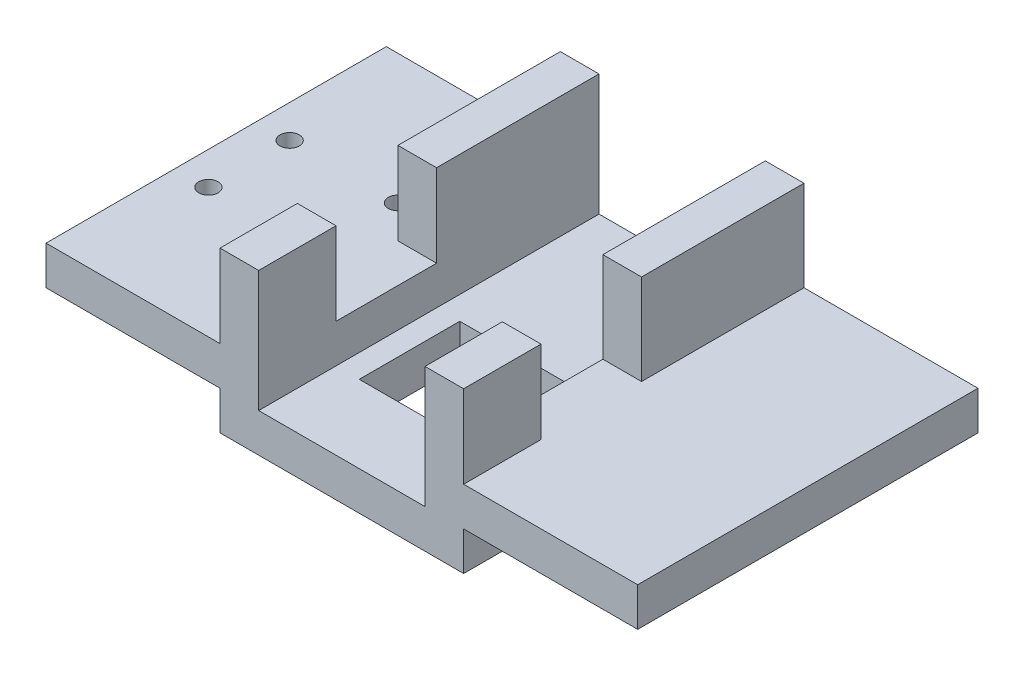
SolidWorks part; units mm, degrees
ref_plane "Plan de face" through (0, 0, 0) normal (0, 0, 1) x (1, 0, 0)
ref_plane "Plan de dessus" through (0, 0, 0) normal (0, 1, 0) x (1, 0, 0)
ref_plane "Plan de droite" through (0, 0, 0) normal (1, 0, 0) x (0, 0, -1)
sketch "Sketch1" plane through (0, 0, 0) normal (0, 0, 1) x (1, 0, 0)
  line L1 (0, -4.1444) -> (10, -4.1444)
  line L2 (10, -4.1444) -> (10, -35.5315)
  line L3 (0, -4.1444) -> (0, -25.5315)
  line L4 (63, -45.5315) -> (0, -45.5315)
  line L5 (0, -25.5315) -> (-45, -25.5315)
  line L6 (10, -35.5315) -> (53, -35.5315)
  line L7 (53, -35.5315) -> (53, -2.1133)
  line L8 (53, -2.1133) -> (63, -2.1133)
  line L9 (-45, -25.5315) -> (-45, -35.5315)
  line L10 (-45, -35.5315) -> (0, -35.5315)
  line L11 (0, -35.5315) -> (0, -45.5315)
  line L12 (63, -2.1133) -> (63, -25.5315)
  line L13 (63, -25.5315) -> (108, -25.5315)
  line L14 (108, -25.5315) -> (108, -35.5315)
  line L15 (108, -35.5315) -> (63, -35.5315)
  line L16 (63, -35.5315) -> (63, -45.5315)
  dimension "D1" = 10
  dimension "D2" = 10
  dimension "D3" = 43
  dimension "D4" = 10
  dimension "D5" = 10
  dimension "D6" = 10
  dimension "D7" = 45
  dimension "D8" = 45
extrude "Boss-Extrude1" add sketch "Sketch1" along normal blind 42
sketch "Sketch2" plane through (0, 0, 42) normal (0, 0, 1) x (1, 0, 0)
  line L0 (-45, -35.5315) -> (0, -35.5315) construction
  line L1 (-45, -25.5315) -> (10, -25.5315)
  line L2 (-45, -25.5315) -> (-45, -35.5315)
  line L3 (-45, -35.5315) -> (0, -35.5315)
  line L4 (0, -35.5315) -> (0, -45.5315)
  line L5 (0, -45.5315) -> (16, -45.5315)
  line L6 (53, -25.5315) -> (108, -25.5315)
  line L7 (0, -45.5315) -> (63, -45.5315) construction
  line L8 (63, -35.5315) -> (108, -35.5315)
  line L9 (108, -25.5315) -> (108, -35.5315)
  line L10 (16, -45.5315) -> (16, -35.5315)
  line L11 (53, -35.5315) -> (10, -35.5315) construction
  line L12 (16, -35.5315) -> (10, -35.5315)
  line L13 (10, -35.5315) -> (10, -25.5315)
  line L14 (10, -35.5315) -> (10, -4.1444) construction
  line L15 (63, -35.5315) -> (63, -45.5315)
  line L16 (63, -45.5315) -> (47, -45.5315)
  line L17 (47, -45.5315) -> (47, -35.5315)
  line L18 (47, -35.5315) -> (53, -35.5315)
  line L19 (53, -35.5315) -> (53, -25.5315)
  line L20 (53, -2.1133) -> (53, -35.5315) construction
  dimension "D1" = 16
  dimension "D2" = 10
  dimension "D3" = 16
extrude "Boss-Extrude2" add sketch "Sketch2" along normal blind 46
sketch "Sketch3" plane through (47, 0, 0) normal (-1, 0, 0) x (0, 0, 1)
  line L0 (88, -45.5315) -> (42, -45.5315) construction
  line L1 (88, -35.5315) -> (68, -35.5315)
  line L2 (88, -35.5315) -> (88, -45.5315)
  line L3 (88, -45.5315) -> (68, -45.5315)
  line L4 (68, -35.5315) -> (68, -45.5315)
  dimension "D1" = 20
extrude "Boss-Extrude3" add sketch "Sketch3" along normal up to surface (31 mm away) up to face at (16, -41.7815, 76.5)
sketch "Sketch4" plane through (0, -25.5315, 0) normal (0, 1, 0) x (1, 0, 0)
  line L0 (108, -88) -> (53, -88) construction
  line L1 (10, -88) -> (0, -88)
  line L2 (10, -88) -> (10, -68)
  line L3 (10, -68) -> (0, -68)
  line L4 (0, -88) -> (0, -68)
  line L5 (63, -88) -> (53, -88)
  line L6 (63, -88) -> (63, -68)
  line L7 (63, -68) -> (53, -68)
  line L8 (53, -88) -> (53, -68)
  line L9 (53, -88) -> (53, -42) construction
  dimension "D1" = 20
  dimension "D2" = 20
  dimension "D3" = 10
  dimension "D4" = 10
extrude "Boss-Extrude4" add sketch "Sketch4" along normal up to surface (21.3872 mm away) up to face at (5, -4.1444, 21)
sketch "Sketch5" plane through (0, -25.5315, 0) normal (0, 1, 0) x (1, 0, 0)
  line L0 (-45, -88) -> (0, 0) construction
  line L1 (0, -88) -> (-45, 0) construction
  point P4 (-22.5, -44)
sketch "Sketch6" plane through (0, -25.5315, 0) normal (0, 1, 0) x (1, 0, 0)
  line L1 (-22.5, -44) -> (-22.5, -77.5396) construction
  line L2 (-22.5, -44) -> (-5.5326, -44) construction
  line L3 (-0.0537, -140.2525) -> (-0.0537, -9) construction
  line L4 (-0.0537, -119.2525) -> (-0.0537, -161.2525) construction
  circle A0 centre (-36.5, -54.5) radius 2.5
  circle A1 centre (-8.5, -54.5) radius 2.5
  circle A2 centre (-36.5, -33.5) radius 2.5
  circle A3 centre (-8.5, -33.5) radius 2.5
  circle A4 centre (-8.5, -54.5) radius 2.5
  circle A5 centre (-36.5, -54.5) radius 2.5
  circle A6 centre (-8.5, -33.5) radius 2.5
  circle A7 centre (-36.5, -33.5) radius 2.5
  circle A8 centre (-36.5, -54.5) radius 2.5
  circle A9 centre (-8.5, -54.5) radius 2.5
  circle A10 centre (-36.5, -33.5) radius 2.5
  circle A11 centre (-8.5, -33.5) radius 2.5
  circle A12 centre (-8.5, -54.5) radius 2.5
  circle A13 centre (-36.5, -54.5) radius 2.5
  circle A14 centre (-8.5, -33.5) radius 2.5
  circle A15 centre (-36.5, -33.5) radius 2.5
  dimension "D1" = 5
  dimension "D2" = 10.5
  dimension "D3" = 14
extrude "Cut-Extrude1" cut sketch "Sketch6" against normal through all
